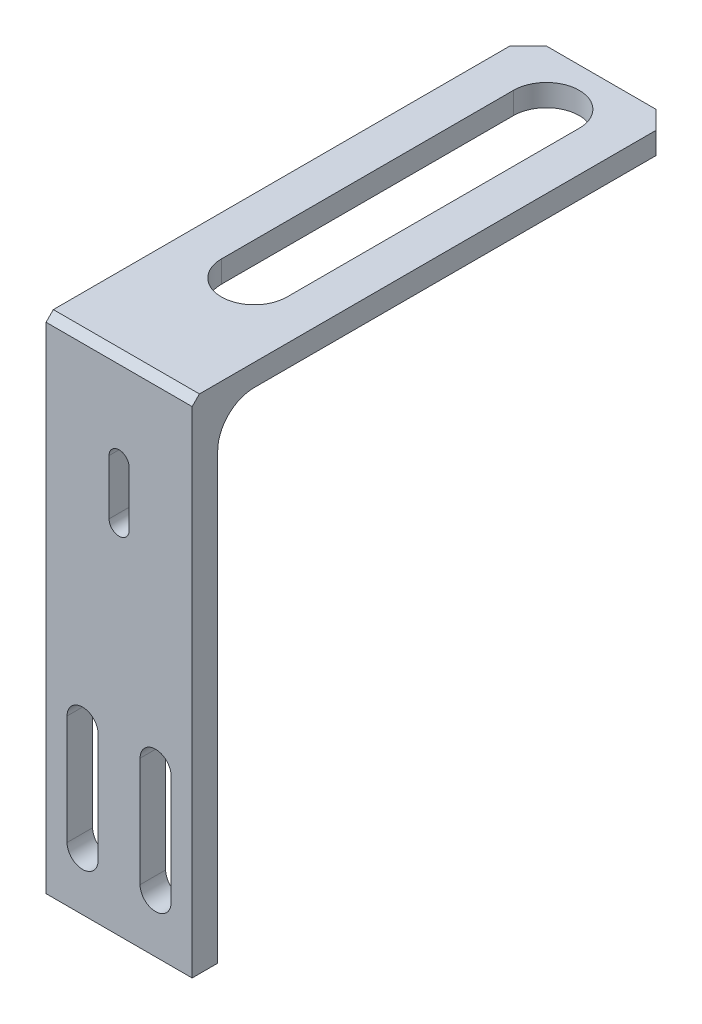
SolidWorks part; units mm, degrees
ref_plane "Front Plane" through (0, 0, 0) normal (0, 0, 1) x (1, 0, 0)
ref_plane "Top Plane" through (0, 0, 0) normal (0, 1, 0) x (1, 0, 0)
ref_plane "Right Plane" through (0, 0, 0) normal (1, 0, 0) x (0, 0, -1)
sketch "Sketch1" plane through (0, 0, 0) normal (0, 0, 1) x (1, 0, 0)
  line L0 (0, -298.4187) -> (0, 14622.5169) construction
  line L1 (-298.4187, 0) -> (14622.5169, 0) construction
  line L2 (-30, -22.5) -> (-30, 22.5) construction
  line L3 (-30, 22.5) -> (30, 22.5) construction
  line L4 (30, 22.5) -> (30, -22.5) construction
  line L5 (-30, -22.5) -> (30, -22.5) construction
  line L6 (-30, 22.5) -> (-30, 43.5) construction
  line L7 (-30, 43.5) -> (30, 43.5) construction
  line L8 (30, 43.5) -> (30, 22.5) construction
  line L9 (-30, 5) -> (30, 5) construction
  line L10 (-30, -5) -> (30, -5) construction
  line L11 (-30, 26.5) -> (30, 26.5) construction
  point P7 (0, 22.5)
  point P11 (-30, 0)
  point P12 (30, 0)
  dimension "D1" = 22.5
  dimension "D2" = 60
  dimension "D3" = 66
  dimension "D4" = 5
  dimension "D5" = 4
sketch "Sketch2" plane through (0, 0, 0) normal (0, 0, 1) x (1, 0, 0)
  line L0 (0, -200298.4187) -> (0, 214622.5169) construction
  line L1 (-20, -35) -> (20, -35)
  line L2 (-20, -35) -> (-20, 102.5)
  line L3 (-20, 102.5) -> (20, 102.5)
  line L4 (20, -35) -> (20, 102.5)
  line L5 (0, -1000) -> (0, 49000) construction
  line L6 (-995.2529, 0) -> (48885.9273, 0) construction
  line L8 (-10, 10) -> (-10, -20) construction
  line L9 (-5.75, 10) -> (-5.75, -20)
  line L10 (-14.25, 10) -> (-14.25, -20)
  line L11 (10, 10) -> (10, -20) construction
  line L12 (5.75, 10) -> (5.75, -20)
  line L13 (14.25, 10) -> (14.25, -20)
  line L14 (-30, 26.5) -> (30, 26.5) construction
  line L15 (0, 77.5) -> (0, 62.5) construction
  line L16 (2.75, 77.5) -> (2.75, 62.5)
  line L17 (-2.75, 77.5) -> (-2.75, 62.5)
  arc A0 (-5.75, 10) -> (-14.25, 10) centre (-10, 10) ccw
  arc A1 (-14.25, -20) -> (-5.75, -20) centre (-10, -20) ccw
  arc A2 (5.75, 10) -> (14.25, 10) centre (10, 10) cw
  arc A3 (14.25, -20) -> (5.75, -20) centre (10, -20) cw
  arc A4 (2.75, 77.5) -> (-2.75, 77.5) centre (0, 77.5) ccw
  arc A5 (-2.75, 62.5) -> (2.75, 62.5) centre (0, 62.5) ccw
  point P6 (0, -35)
  point P14 (-10, -5)
  point P21 (10, -5)
  point P30 (0, 70)
  dimension "D1" = 8.5
  dimension "D2" = 40
  dimension "D3" = 10
  dimension "D4" = 30
  dimension "D5" = 15
  dimension "D6" = 35
  dimension "D7" = 76
  dimension "D8" = 5.5
  dimension "D9" = 15
  dimension "D10" = 25
extrude "Boss-Extrude1" add sketch "Sketch2" along normal blind 7
sketch "Sketch4" plane through (0, 102.5, 0) normal (0, 1, 0) x (1, 0, 0)
  line L0 (-20, 0) -> (-20, 125)
  line L1 (0, -1000) -> (0, 49000) construction
  line L2 (-20, 125) -> (20, 125)
  line L3 (20, 125) -> (20, 0)
  line L4 (20, 0) -> (-20, 0)
  line L5 (0, 30) -> (0, 110) construction
  line L6 (-9, 30) -> (-9, 110)
  line L7 (9, 30) -> (9, 110)
  arc A0 (-9, 30) -> (9, 30) centre (0, 30) ccw
  arc A1 (9, 110) -> (-9, 110) centre (0, 110) ccw
  point P11 (0, 70)
  point P16 (0, 15.4243)
  dimension "D1" = 18
  dimension "D2" = 80
  dimension "D3" = 30
  dimension "D4" = 15
extrude "Boss-Extrude2" add sketch "Sketch4" against normal blind 6
fillet "Fillet1" radius 10 1 edges at (0, 96.5, 0)
chamfer "Chamfer1" distance 5 angle 45 2 edges at (20, 99.5, -125) (-20, 99.5, -125)
chamfer "Chamfer2" distance 2 angle 45 1 edges at (0, 102.5, 7)
